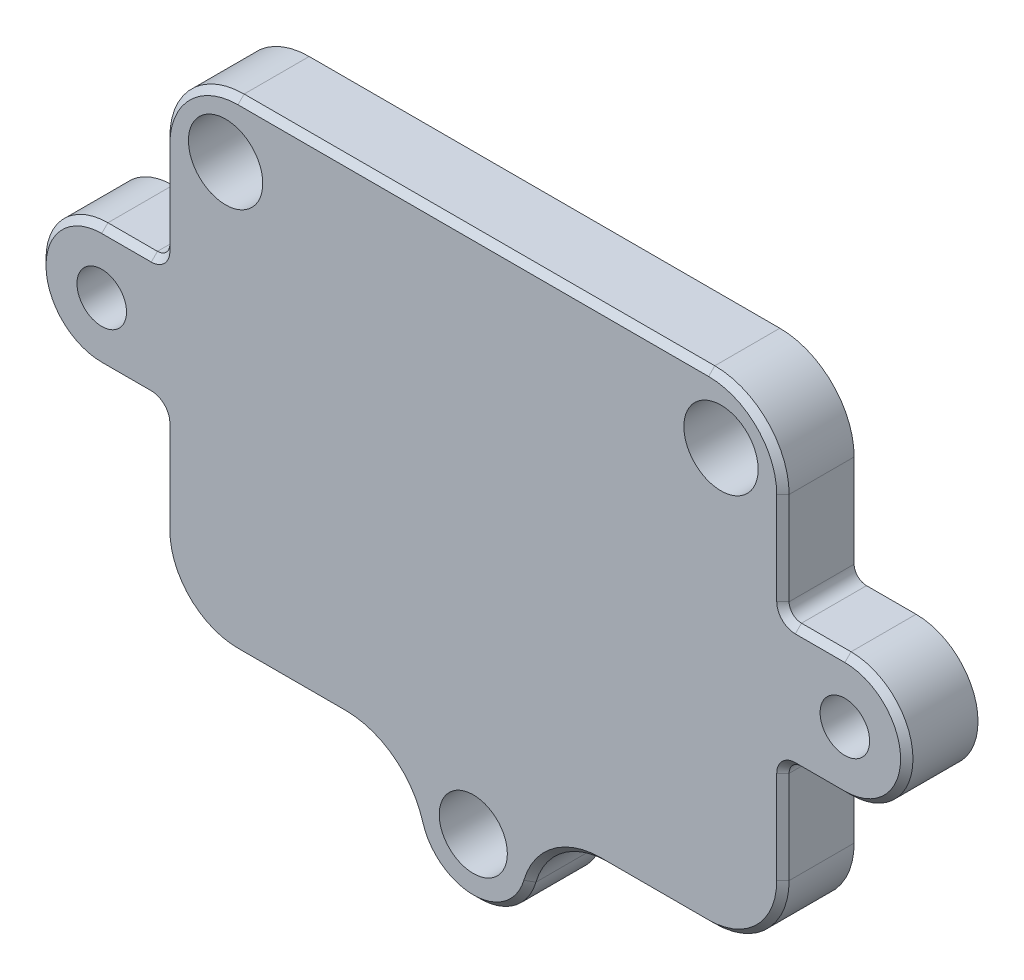
SolidWorks part; units mm, degrees
ref_plane "Front Plane" through (0, 0, 0) normal (0, 0, 1) x (1, 0, 0)
ref_plane "Top Plane" through (0, 0, 0) normal (0, 1, 0) x (1, 0, 0)
ref_plane "Right Plane" through (0, 0, 0) normal (1, 0, 0) x (0, 0, -1)
sketch "Sketch1" plane through (0, 0, 0) normal (0, 0, 1) x (1, 0, 0)
  line L0 (0, 0) -> (0, -42) construction
  line L1 (-19, 0) -> (19, 0) construction
  line L3 (-19, 0) -> (19, 0)
  line L21 (19, 0) -> (-19, 0)
  line L26 (-25, -6) -> (-25, -13.5)
  line L27 (-26, -14.5) -> (-30, -14.5)
  line L28 (-30, -24.5) -> (-26, -24.5)
  line L29 (-25, -25.5) -> (-25, -33)
  line L30 (-19, -39) -> (-10.3229, -39)
  line L33 (10.3229, -39) -> (19, -39)
  line L34 (25, -33) -> (25, -25.5)
  line L35 (26, -24.5) -> (30, -24.5)
  line L36 (30, -14.5) -> (26, -14.5)
  line L37 (25, -13.5) -> (25, -6)
  line L42 (19, 0) -> (-19, 0)
  line L47 (-25, -6) -> (-25, -13.5)
  line L48 (-26, -14.5) -> (-30, -14.5)
  line L49 (-30, -24.5) -> (-26, -24.5)
  line L50 (-25, -25.5) -> (-25, -33)
  line L51 (-19, -39) -> (-10.3229, -39)
  line L54 (10.3229, -39) -> (19, -39)
  line L55 (25, -33) -> (25, -25.5)
  line L56 (26, -24.5) -> (30, -24.5)
  line L57 (30, -14.5) -> (26, -14.5)
  line L58 (25, -13.5) -> (25, -6)
  arc A2 (19, 0) -> (25, -6) centre (19, -6) cw
  circle A3 centre (20, -5) radius 3
  circle A4 centre (30, -19.5) radius 2 construction
  circle A5 centre (-30, -19.5) radius 2 construction
  circle A6 centre (30, -19.5) radius 2
  circle A7 centre (-30, -19.5) radius 2
  circle A8 centre (0, -42) radius 2.75 construction
  circle A11 centre (0, -42) radius 2.75
  circle A13 centre (-20, -5) radius 3
  arc A17 (-19, 0) -> (-25, -6) centre (-19, -6) ccw
  arc A18 (-19, 0) -> (-25, -6) centre (-19, -6) ccw
  arc A19 (25, -6) -> (19, 0) centre (19, -6) ccw
  arc A20 (-26, -14.5) -> (-25, -13.5) centre (-26, -13.5) ccw
  arc A21 (-30, -14.5) -> (-30, -24.5) centre (-30, -19.5) ccw
  arc A22 (-25, -25.5) -> (-26, -24.5) centre (-26, -25.5) ccw
  arc A23 (-25, -33) -> (-19, -39) centre (-19, -33) ccw
  arc A24 (-4.5613, -43.3256) -> (-10.3229, -39) centre (-10.3229, -45) ccw
  arc A25 (-4.5613, -43.3256) -> (4.5613, -43.3256) centre (0, -42) ccw
  arc A26 (10.3229, -39) -> (4.5613, -43.3256) centre (10.3229, -45) ccw
  arc A27 (19, -39) -> (25, -33) centre (19, -33) ccw
  arc A28 (26, -24.5) -> (25, -25.5) centre (26, -25.5) ccw
  arc A29 (30, -24.5) -> (30, -14.5) centre (30, -19.5) ccw
  arc A30 (25, -13.5) -> (26, -14.5) centre (26, -13.5) ccw
  arc A37 (-26, -14.5) -> (-25, -13.5) centre (-26, -13.5) ccw
  arc A38 (-30, -14.5) -> (-30, -24.5) centre (-30, -19.5) ccw
  arc A39 (-25, -25.5) -> (-26, -24.5) centre (-26, -25.5) ccw
  arc A40 (-25, -33) -> (-19, -39) centre (-19, -33) ccw
  arc A41 (-4.5613, -43.3256) -> (-10.3229, -39) centre (-10.3229, -45) ccw
  arc A42 (-4.5613, -43.3256) -> (4.5613, -43.3256) centre (0, -42) ccw
  arc A43 (10.3229, -39) -> (4.5613, -43.3256) centre (10.3229, -45) ccw
  arc A44 (19, -39) -> (25, -33) centre (19, -33) ccw
  arc A45 (26, -24.5) -> (25, -25.5) centre (26, -25.5) ccw
  arc A46 (30, -24.5) -> (30, -14.5) centre (30, -19.5) ccw
  arc A47 (25, -13.5) -> (26, -14.5) centre (26, -13.5) ccw
  dimension "D2" = 6
  dimension "D3" = 5
  dimension "D4" = 5
  dimension "D1" = 0
extrude "Boss-Extrude1" add sketch "Sketch1" along normal blind 5.75
chamfer "Chamfer1" distance 0.5 angle 45 24 edges at (-25, -9.75, 5.75) (-25.2929, -14.2071, 5.75) (-28, -14.5, 5.75) (-35, -19.5, 5.75) (-28, -24.5, 5.75) (-25.2929, -24.7929, 5.75) (-25, -29.25, 5.75) (-23.2426, -37.2426, 5.75) (-14.6615, -39, 5.75) (-6.7206, -40.2017, 5.75) (0, -46.75, 5.75) (6.7206, -40.2017, 5.75) (14.6615, -39, 5.75) (23.2426, -37.2426, 5.75) (25, -29.25, 5.75) (25.2929, -24.7929, 5.75) (28, -24.5, 5.75) (35, -19.5, 5.75) (28, -14.5, 5.75) (25.2929, -14.2071, 5.75) (25, -9.75, 5.75) (0, 0, 5.75) (-23.2426, -1.7574, 5.75) (23.2426, -1.7574, 5.75)
